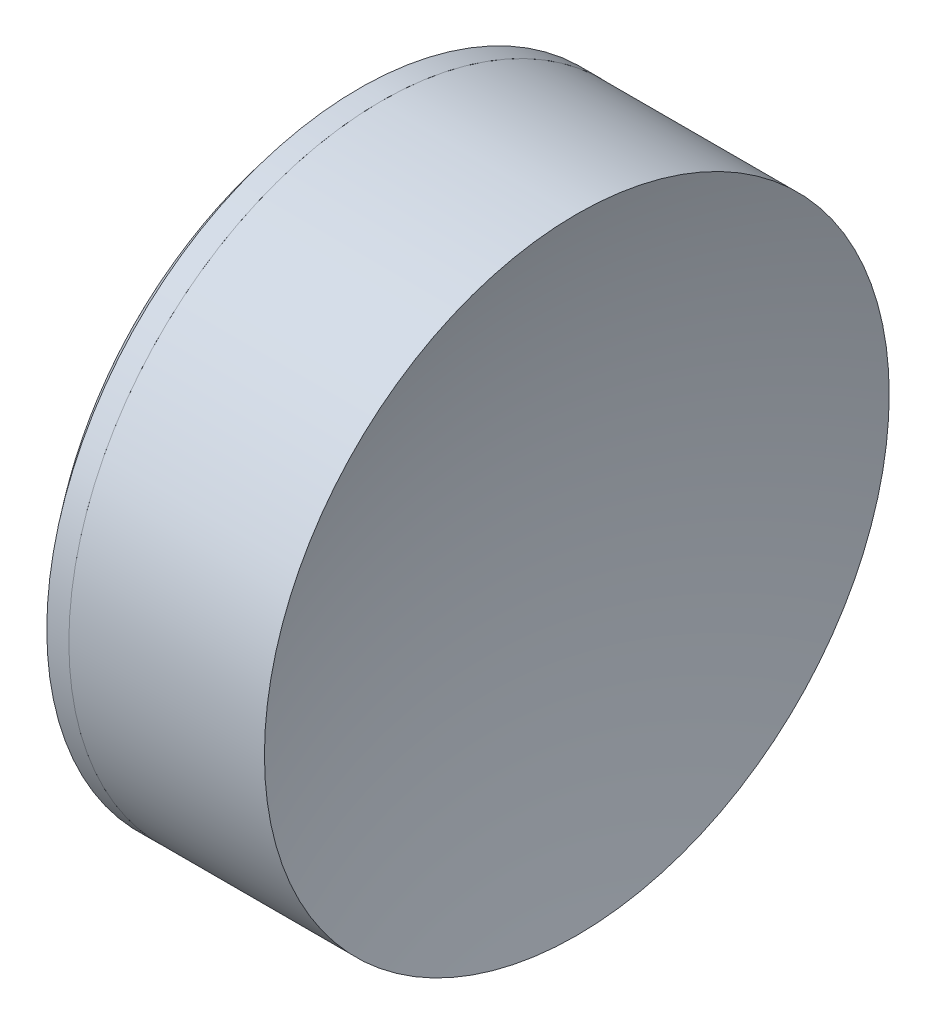
SolidWorks part; units mm, degrees
ref_plane "前视基准面" through (0, 0, 0) normal (0, 0, 1) x (1, 0, 0)
ref_plane "上视基准面" through (0, 0, 0) normal (0, 1, 0) x (1, 0, 0)
ref_plane "右视基准面" through (0, 0, 0) normal (1, 0, 0) x (0, 0, -1)
sketch "草图1" plane through (0, 0, 0) normal (0, 1, 0) x (1, 0, 0)
  line L0 (-0.8161, 0) -> (118.0272, 0) construction
  line L1 (102.5051, -25.4) -> (104.2995, -25.4)
  line L2 (102.5051, 25.4) -> (104.2995, 25.4)
  arc A0 (104.2995, -25.4) -> (104.2995, 25.4) centre (61.3594, 0) ccw
  arc A1 (102.5051, 25.4) -> (102.5051, -25.4) centre (132.7294, 0) ccw
  point P10 (93.2494, 0)
  point P11 (111.2494, 0)
  dimension "D3" = 39.48
  dimension "D4" = 49.89
  dimension "D1" = 25.4
  dimension "D2" = 25.4
  dimension "D5" = 18
revolve "旋转1" add sketch "草图1" angle 360 about L0
sketch "草图2" plane through (0, 0, 0) normal (0, 1, 0) x (1, 0, 0)
  line L0 (-0.5519, 0) -> (162.8134, 0) construction
  line L2 (104.2995, 25.4) -> (120.2015, 25.4)
  line L3 (104.2995, -25.4) -> (120.2015, -25.4)
  arc A0 (120.2015, 25.4) -> (120.2015, -25.4) centre (199.8494, 0) ccw
  arc A1 (104.2995, -25.4) -> (104.2995, 25.4) centre (61.3594, 0) ccw construction
  arc A2 (104.2995, -25.4) -> (104.2995, 25.4) centre (61.3594, 0) ccw
  point P4 (111.2494, 0)
  point P8 (116.2494, 0)
  dimension "D1" = 83.6
  dimension "D2" = 5
revolve "旋转2" add sketch "草图2" angle 360 about L0
